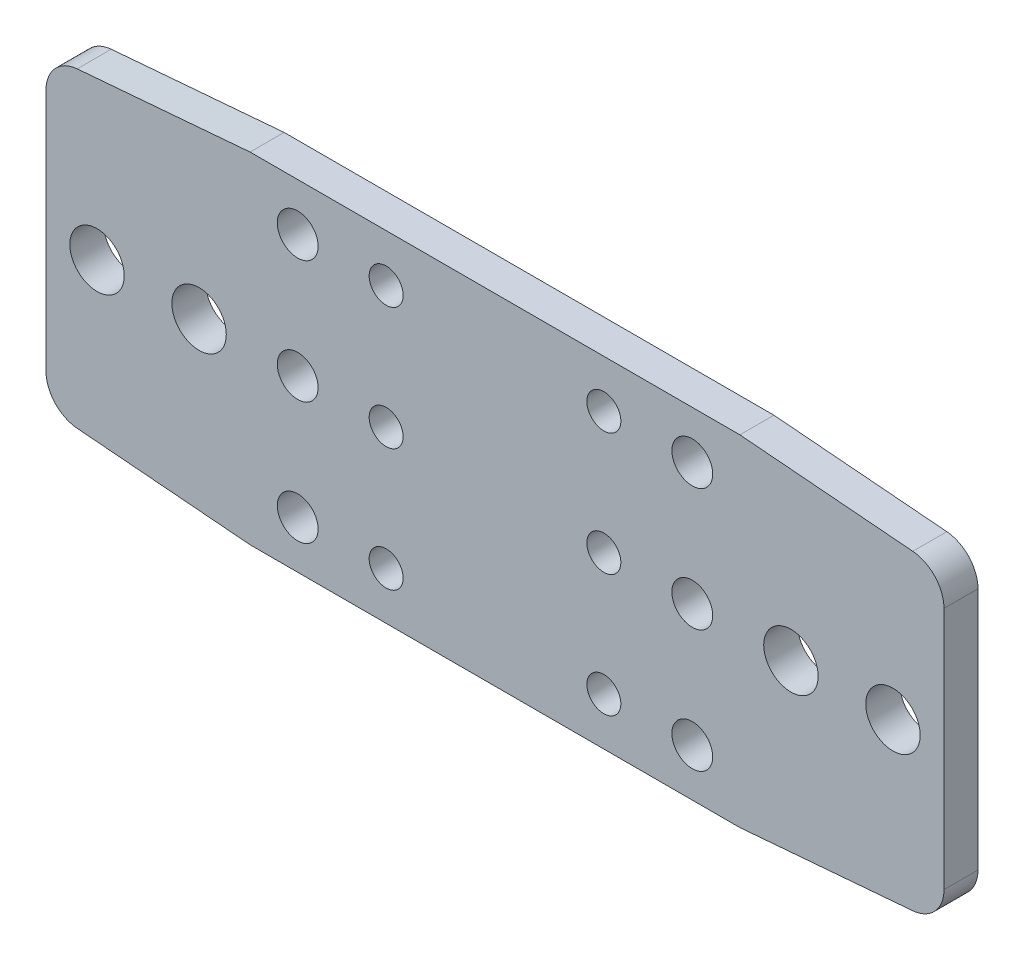
SolidWorks part; units mm, degrees
ref_plane "Płaszczyzna przednia" through (0, 0, 0) normal (0, 0, 1) x (1, 0, 0)
ref_plane "Płaszczyzna górna" through (0, 0, 0) normal (0, 1, 0) x (1, 0, 0)
ref_plane "Płaszczyzna prawa" through (0, 0, 0) normal (1, 0, 0) x (0, 0, -1)
sketch "Sketch1" plane through (0, 0, 0) normal (0, 0, 1) x (1, 0, 0)
  line L0 (0, -25) -> (72, -25) construction
  line L1 (36, 0) -> (36, -50) construction
  line L2 (7, -43) -> (25.8871, -43) construction
  line L3 (65, -7) -> (65, -43) construction
  line L4 (34, 0) -> (34, -50) construction
  line L5 (38, 0) -> (38, -50) construction
  line L6 (20, 0) -> (20, -50) construction
  line L7 (7, -7) -> (7, -25) construction
  line L8 (72, 0) -> (0, 0)
  line L9 (0, 0) -> (0, -50) construction
  line L10 (0, -50) -> (72, -50)
  line L11 (72, -50) -> (72, 0) construction
  line L12 (7, -25) -> (7, -43) construction
  line L13 (7, -7) -> (23.3918, -7) construction
  line L14 (0, -25) -> (-30, -25) construction
  line L15 (-30, -47.5) -> (-30, -2.5)
  line L16 (-30, -2.5) -> (0, 0)
  line L17 (-30, -47.5) -> (0, -50)
  line L18 (-15, -25) -> (-15, -21.253) construction
  line L19 (-22.5, -25) -> (-22.5, -21.253) construction
  line L20 (-7.5, -25) -> (-7.5, -21.253) construction
  line L21 (65, -7) -> (48.6082, -7) construction
  line L22 (52, 0) -> (52, -50) construction
  line L23 (65, -43) -> (46.1129, -43) construction
  line L24 (72, -25) -> (102, -25) construction
  line L25 (102, -47.5) -> (72, -50)
  line L26 (102, -2.5) -> (72, 0)
  line L27 (79.5, -25) -> (79.5, -21.253) construction
  line L28 (94.5, -25) -> (94.5, -21.253) construction
  line L29 (87, -25) -> (87, -21.253) construction
  line L30 (102, -47.5) -> (102, -2.5)
  circle A0 centre (-22.5, -25) radius 4
  circle A1 centre (-7.5, -25) radius 4
  circle A2 centre (52, -43) radius 2.5
  circle A3 centre (52, -7) radius 2.5
  circle A4 centre (79.5, -25) radius 4
  circle A5 centre (94.5, -25) radius 4
  circle A6 centre (20, -25) radius 2.5
  circle A7 centre (52, -25) radius 2.5
  arc A12 (7, -40) -> (7, -46) centre (7, -43) ccw
  arc A13 (7, -46) -> (7, -40) centre (7, -43) ccw
  arc A16 (65, -46) -> (65, -40) centre (65, -43) ccw
  arc A17 (65, -40) -> (65, -46) centre (65, -43) ccw
  arc A18 (65, -10) -> (65, -4) centre (65, -7) ccw
  arc A19 (65, -4) -> (65, -10) centre (65, -7) ccw
  arc A22 (7, -10) -> (7, -4) centre (7, -7) ccw
  arc A23 (7, -4) -> (7, -10) centre (7, -7) ccw
  circle A24 centre (7, -25) radius 3
  circle A25 centre (65, -25) radius 3
  circle A28 centre (20, -7) radius 2.5
  circle A29 centre (20, -43) radius 2.5
  point P40 (-30, -25)
  point P67 (102, -25)
  dimension "D3" = 3
  dimension "D6" = 6
  dimension "D7" = 6
  dimension "D11" = 5
  dimension "D12" = 5
  dimension "D17" = 8
  dimension "D18" = 8
  dimension "D19" = 5
  dimension "D20" = 5
  dimension "D1" = 72
  dimension "D2" = 50
  dimension "D4" = 7
  dimension "D5" = 7
  dimension "D10" = 20
  dimension "D13" = 30
  dimension "D14" = 45
  dimension "D8" = 2
  dimension "D9" = 2
  dimension "D15" = 7.5
  dimension "D16" = 7.5
extrude "Boss-Extrude1" add sketch "Sketch1" along normal blind 5
fillet "Fillet1" radius 5 4 edges at (102, -2.5, 2.5) (102, -47.5, 2.5) (-30, -2.5, 2.5) (-30, -47.5, 2.5)
